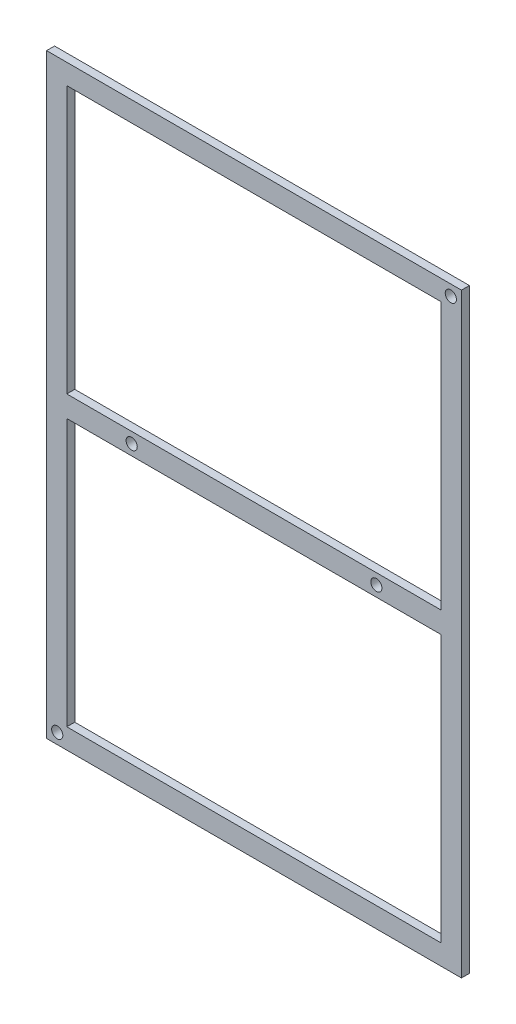
SolidWorks part; units mm, degrees
ref_plane "Front Plane" through (0, 0, 0) normal (0, 0, 1) x (1, 0, 0)
ref_plane "Top Plane" through (0, 0, 0) normal (0, 1, 0) x (1, 0, 0)
ref_plane "Right Plane" through (0, 0, 0) normal (1, 0, 0) x (0, 0, -1)
sketch "Sketch1" plane through (0, 0, 0) normal (0, 0, 1) x (1, 0, 0)
  line L0 (-39, 56) -> (39, -56) construction
  line L1 (-39, 56) -> (39, 56)
  line L2 (-39, 56) -> (-39, -56)
  line L3 (-39, -56) -> (39, -56)
  line L4 (39, 56) -> (39, -56)
  line L9 (-35.2, 52.2) -> (35.2, 52.2)
  line L10 (35.2, 52.2) -> (35.2, -52.2)
  line L11 (-35.2, -52.2) -> (35.2, -52.2)
  line L12 (-35.2, 52.2) -> (-35.2, -52.2)
  dimension "D1" = 112
  dimension "D2" = 78
  dimension "D3" = 3.8
extrude "Boss-Extrude1" add sketch "Sketch1" along normal blind 1.5 contours L1 L0 L12 L9 L10 L4 | L0 L2 L3 L10 L11 L12
sketch "Sketch2" plane through (0, 0, 1.5) normal (0, 0, 1) x (1, 0, 0)
  line L0 (0, 0) -> (-17.6757, 0) construction
  line L1 (-35.2, 2) -> (35.2, 2)
  line L2 (-35.2, 52.2) -> (-35.2, -52.2) construction
  line L3 (35.2, 52.2) -> (35.2, -52.2) construction
  line L4 (35.2, 2) -> (35.2, -2)
  line L5 (-35.2, 2) -> (-35.2, -2)
  line L6 (-35.2, -2) -> (35.2, -2)
  point P13 (35.2, 0)
  point P14 (-35.2, 0)
  dimension "D1" = 2
extrude "Boss-Extrude3" add sketch "Sketch2" against normal up to surface (1.5 mm away) up to face at (0, 0, 0)
sketch "Sketch4" plane through (0, 0, 1.5) normal (0, 0, 1) x (1, 0, 0)
  line L0 (-39, 56) -> (39, 56) construction
  line L1 (39, 56) -> (39, -56) construction
  line L2 (-39, 56) -> (-39, -56) construction
  line L3 (-39, -56) -> (39, -56) construction
  circle A0 centre (37, 54) radius 1.05
  circle A1 centre (23, 0) radius 1.05
  circle A2 centre (-23, 0) radius 1.05
  circle A3 centre (-37, -54) radius 1.05
  dimension "D3" = 2.1
  dimension "D4" = 16
  dimension "D1" = 2
  dimension "D2" = 2
  dimension "D5" = 16
  dimension "D6" = 2
  dimension "D7" = 2
extrude "Cut-Extrude1" cut sketch "Sketch4" against normal through all
